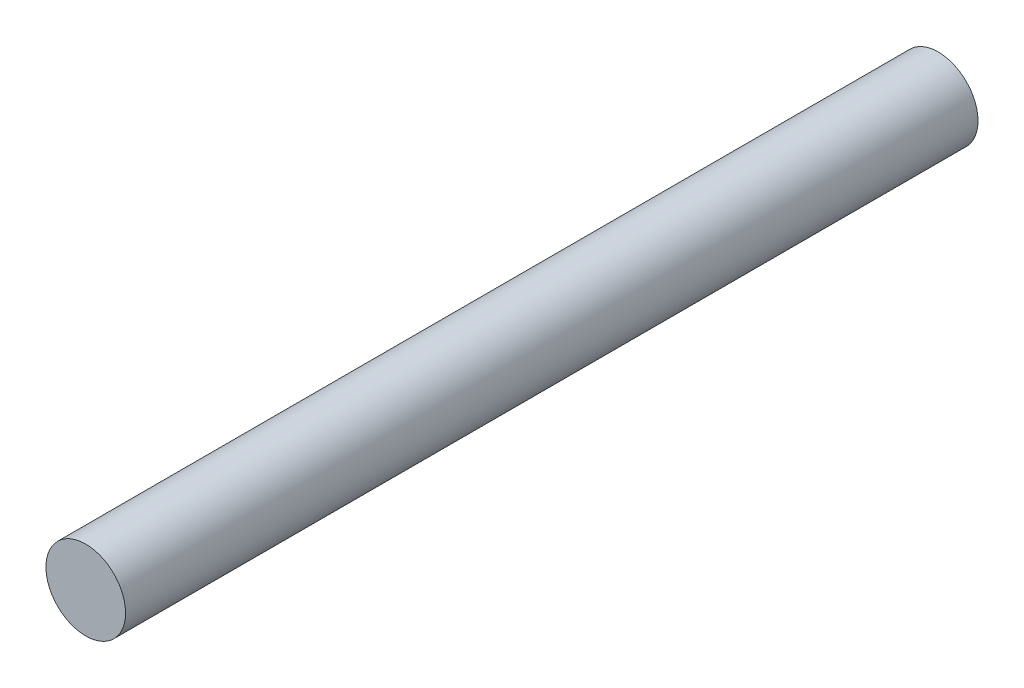
SolidWorks part; units mm, degrees
ref_plane "Front Plane" through (0, 0, 0) normal (0, 0, 1) x (1, 0, 0)
ref_plane "Top Plane" through (0, 0, 0) normal (0, 1, 0) x (1, 0, 0)
ref_plane "Right Plane" through (0, 0, 0) normal (1, 0, 0) x (0, 0, -1)
sketch "Sketch1" plane through (0, 0, 0) normal (0, 0, 1) x (1, 0, 0)
  circle A0 centre (-139.0118, -69.83) radius 3
extrude "Boss-Extrude1" add sketch "Sketch1" along normal blind 64.24
